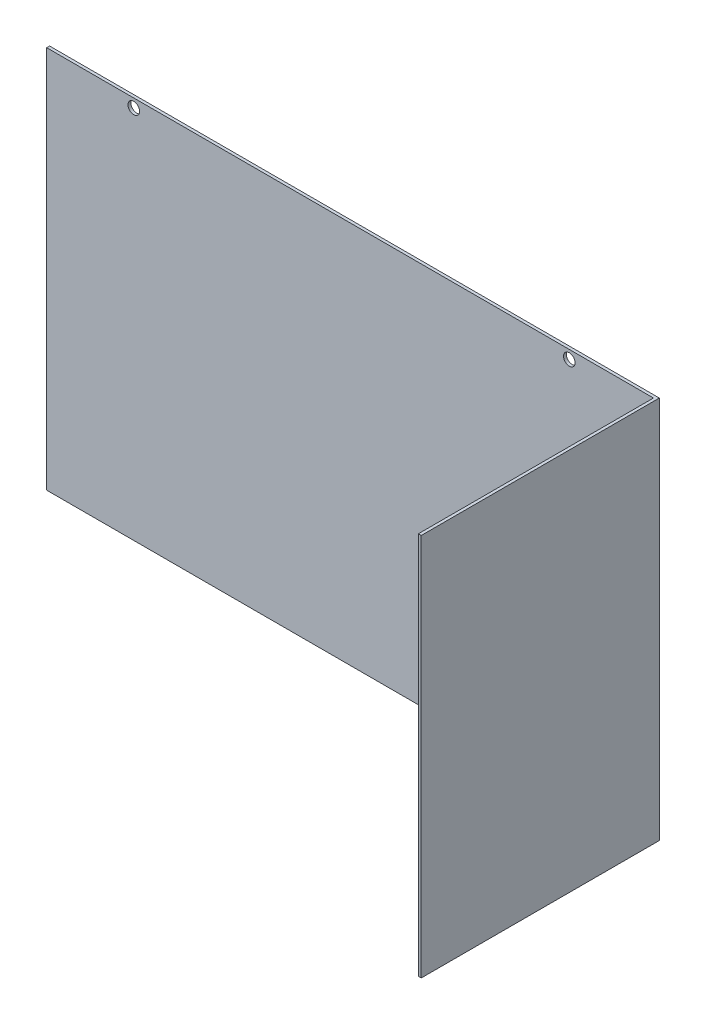
SolidWorks part; units mm, degrees
material "普通碳钢"
ref_plane "前视" through (0, 0, 0) normal (0, 0, 1) x (1, 0, 0)
ref_plane "上视" through (0, 0, 0) normal (0, 1, 0) x (1, 0, 0)
ref_plane "右视" through (0, 0, 0) normal (1, 0, 0) x (0, 0, -1)
sketch "草图1" plane through (0, 0, 0) normal (0, 0, 1) x (1, 0, 0)
  line L0 (-105, -66) -> (105, -66)
  line L1 (-105, -66) -> (-105, 66)
  line L2 (105, -66) -> (105, 66)
  line L3 (-105, 66) -> (105, 66)
  line L4 (-105, -66) -> (105, 66) construction
  line L5 (105, -66) -> (-105, 66) construction
  point P1 (0, 0)
  dimension "D1" = 132
  dimension "D2" = 210
extrude "凸台-拉伸1" add sketch "草图1" along normal blind 1
sketch "草图3" plane through (0, 0, 1) normal (0, 0, 1) x (1, 0, 0)
  line L0 (105, 66) -> (-105, 66) construction
  line L1 (104, 66) -> (105, 66)
  line L2 (104, 66) -> (104, -66)
  line L3 (104, -66) -> (105, -66)
  line L4 (105, 66) -> (105, -66)
  dimension "D1" = 1
extrude "凸台-拉伸2" add sketch "草图3" along normal blind 81
sketch "草图2" plane through (0, 0, 1) normal (0, 0, 1) x (1, 0, 0)
  line L0 (-75, 63) -> (75, 63) construction
  line L1 (-105, 66) -> (-105, -66) construction
  line L5 (104, 66) -> (-105, 66) construction
  circle A0 centre (-75, 63) radius 2
  circle A1 centre (75, 63) radius 2
  dimension "D1" = 150
  dimension "D4" = 4
  dimension "D5" = 4
  dimension "D2" = 30
  dimension "D3" = 3
extrude "切除-拉伸1" cut sketch "草图2" against normal blind 1
